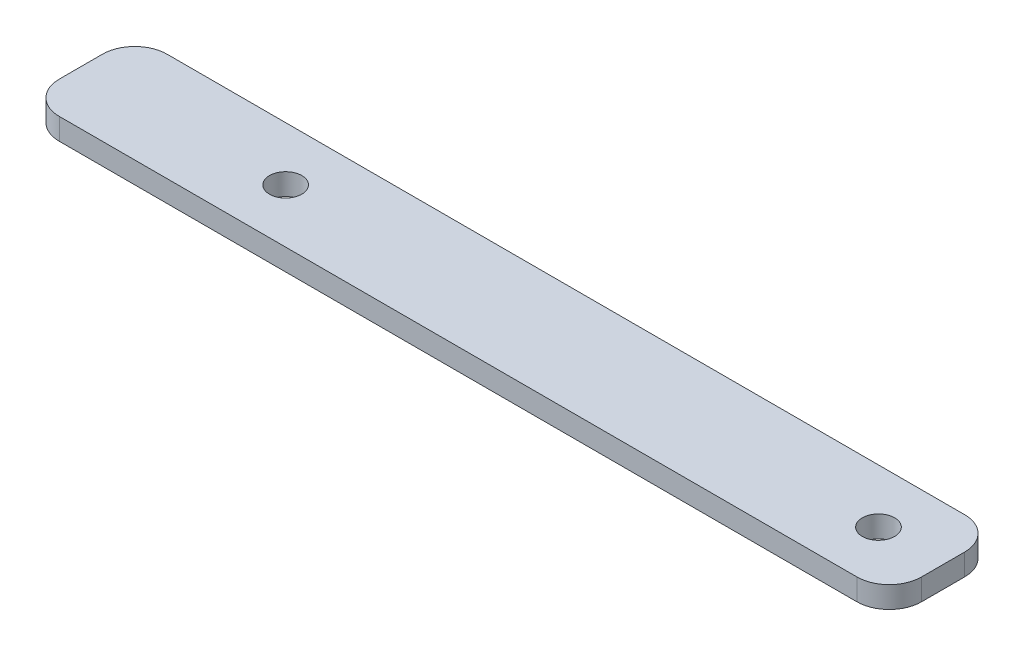
SolidWorks part; units mm, degrees
ref_plane "Front Plane" through (0, 0, 0) normal (0, 0, 1) x (1, 0, 0)
ref_plane "Top Plane" through (0, 0, 0) normal (0, 1, 0) x (1, 0, 0)
ref_plane "Right Plane" through (0, 0, 0) normal (1, 0, 0) x (0, 0, -1)
sketch "Sketch1" plane through (0, 0, 0) normal (0, 1, 0) x (1, 0, 0)
  line L1 (-40, 5) -> (40, 5)
  line L2 (-40, 5) -> (-40, -5)
  line L3 (-40, -5) -> (40, -5)
  line L4 (40, 5) -> (40, -5)
  line L5 (-40, 5) -> (40, -5) construction
  line L6 (-40, -5) -> (40, 5) construction
  point P0 (0, 0)
  dimension "D1" = 10
  dimension "D2" = 80
extrude "Boss-Extrude1" add sketch "Sketch1" along normal blind 2
sketch "Sketch2" plane through (0, 2, 0) normal (0, 1, 0) x (1, 0, 0)
  point P10 (26.3156, 0)
fillet "Fillet1" radius 3 4 edges at (40, 1, 5) (40, 1, -5) (-40, 1, 5) (-40, 1, -5)
hole_wizard "Ø3.0mm Dowel Hole1" positions "Sketch5" profile "Sketch6" hole size "Ø3.0" standard "ISO" end condition through all
sketch "Sketch5" plane through (0, 0, 0) normal (0, -1, 0) x (-1, 0, 0)
  line L1 (-40, -2) -> (-40, 2) construction
  line L3 (40, 0) -> (-40, 0) construction
  line L4 (40, 2) -> (40, -2) construction
  point P0 (-34, 0)
  point P2 (21, 0)
  point P21 (0, 0)
  point P22 (-24, 0)
  dimension "D2" = 6
  dimension "=globalength1" = 55
sketch "Sketch6" plane through (34, 0, 0) normal (1, 0, 0) x (0, 0, -1)
  line L0 (0, 0) -> (0, 2)
  line L1 (0, 2) -> (1.5, 2)
  line L2 (1.5, 2) -> (1.5, 0)
  line L5 (1.5, 0) -> (0, 0)
  line L11 (0, -6.35) -> (0, 107.95) construction
  dimension "Thru Hole Dia." = 3
  dimension "Thru Hole Depth" = 2
equation "\"globalength1\"=55"
